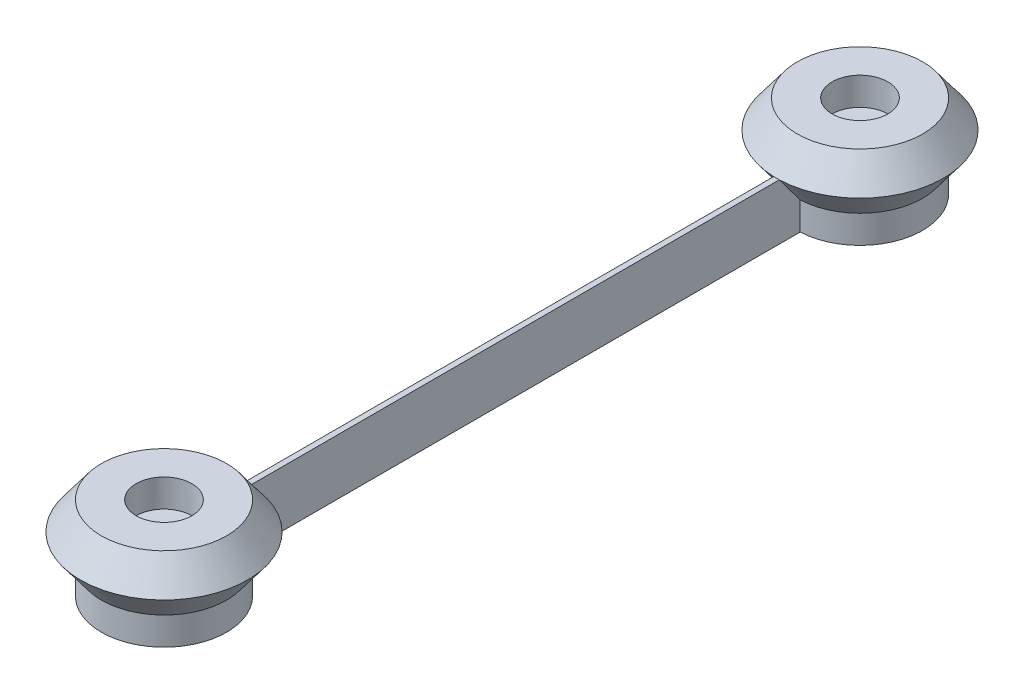
SolidWorks part; units mm, degrees
ref_plane "Front Plane" through (0, 0, 0) normal (0, 0, 1) x (1, 0, 0)
ref_plane "Top Plane" through (0, 0, 0) normal (0, 1, 0) x (1, 0, 0)
ref_plane "Right Plane" through (0, 0, 0) normal (1, 0, 0) x (0, 0, -1)
ref_axis "Axis1" through (0, 55, 0) along (0, -1, 0)
sketch "Sketch1" plane through (0, 0, 0) normal (1, 0, 0) x (0, 0, -1)
  line L0 (1.5, 0) -> (1.5, 8)
  line L1 (1.5, 8) -> (4, 8)
  line L2 (4, 8) -> (4, 12)
  line L3 (4, 12) -> (9, 12)
  line L4 (9, 12) -> (12, 8)
  line L6 (9, 0) -> (1.5, 0)
  line L7 (0, 55) -> (0, -55) construction
  line L8 (9, 0) -> (9, 4)
  line L9 (9, 4) -> (12, 8)
  point P9 (11.2308, 3.145)
  point P11 (9, 3.145)
  point P12 (0, 0)
  point P13 (0, 0)
  dimension "D1" = 4
  dimension "D2" = 1.5
  dimension "D3" = 4
  dimension "D4" = 4
  dimension "D5" = 12
  dimension "D6" = 5
  dimension "D7" = 3
revolve "Revolve1" add sketch "Sketch1" angle 360 about axis through (0, 55, 0) along (0, -1, 0)
ref_plane "Plane1" through (0, 0, -50) normal (0, 0, 1) x (1, 0, 0)
mirror "Mirror2" about plane through (0, 0, -50) normal (0, 0, 1) of bodies 101
sketch "Sketch2" plane through (0, 0, 0) normal (0, 1, 0) x (1, 0, 0)
  line L0 (-40.15, 50) -> (40.15, 50) construction
  line L1 (-0.4, 4) -> (0.4, 4)
  line L2 (-0.4, 4) -> (-0.4, 96)
  line L3 (-0.4, 96) -> (0.4, 96)
  line L4 (0.4, 4) -> (0.4, 96)
  line L5 (0, 96) -> (0, 4) construction
  line L6 (-0.4, 50) -> (0.4, 50) construction
  point P0 (0, 50)
  point P6 (0, 0)
  dimension "D1" = 0.8
extrude "Boss-Extrude1" add sketch "Sketch2" along normal up to vertex
